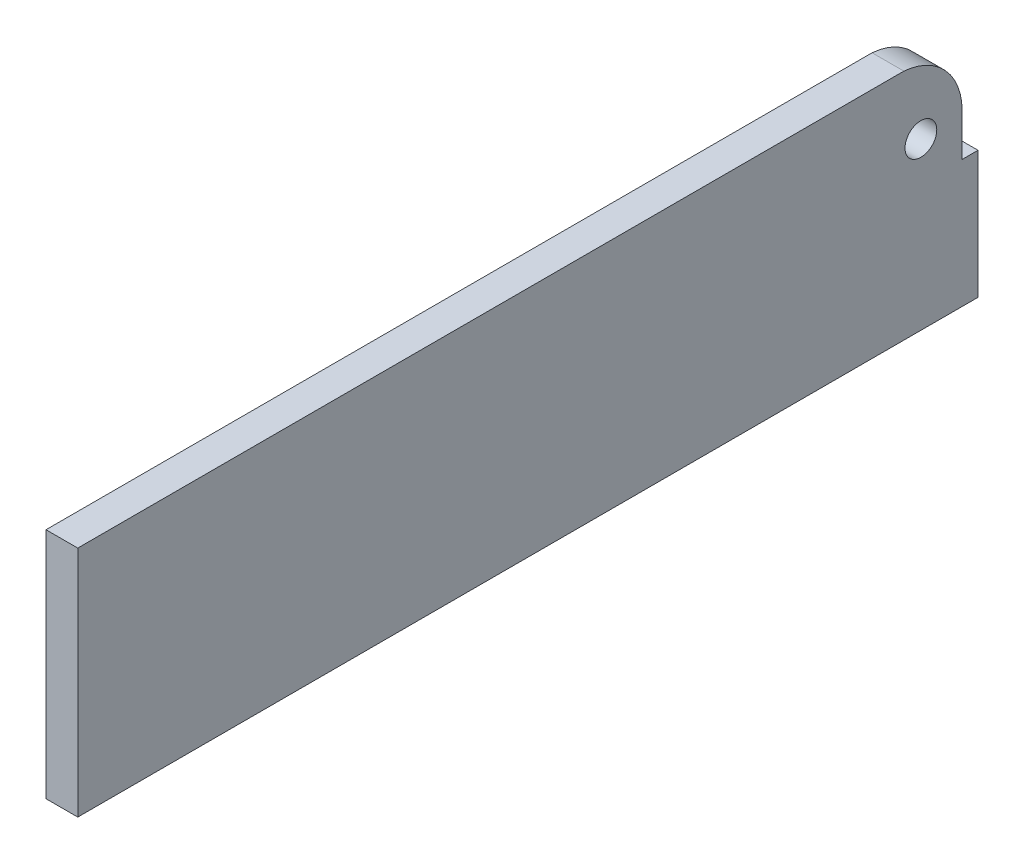
SolidWorks part; units mm, degrees
ref_plane "Front Plane" through (0, 0, 0) normal (0, 0, 1) x (1, 0, 0)
ref_plane "Top Plane" through (0, 0, 0) normal (0, 1, 0) x (1, 0, 0)
ref_plane "Right Plane" through (0, 0, 0) normal (1, 0, 0) x (0, 0, -1)
sketch "Sketch1" plane through (0, 0, 0) normal (1, 0, 0) x (0, 0, -1)
  line L0 (41, 1.5264) -> (42.5, 1.5264)
  line L1 (-42.5, -10.5025) -> (42.5, -10.5025)
  line L2 (-42.5, -10.5025) -> (-42.5, 11.4975)
  line L3 (-42.5, 11.4975) -> (35.5, 11.4975)
  line L4 (42.5, -10.5025) -> (42.5, 1.5264)
  line L5 (41, 1.5264) -> (41, 5.5264)
  circle A0 centre (37.107, 5.1478) radius 1.5
  arc A1 (35.5, 11.4975) -> (41, 5.5264) centre (35.0087, 5.5264) cw
  dimension "D6" = 3
  dimension "D1" = 85
  dimension "D2" = 22
  dimension "D3" = 4
  dimension "D4" = 1.5
  dimension "D5" = 78
extrude "Boss-Extrude1" add sketch "Sketch1" along normal blind 3
